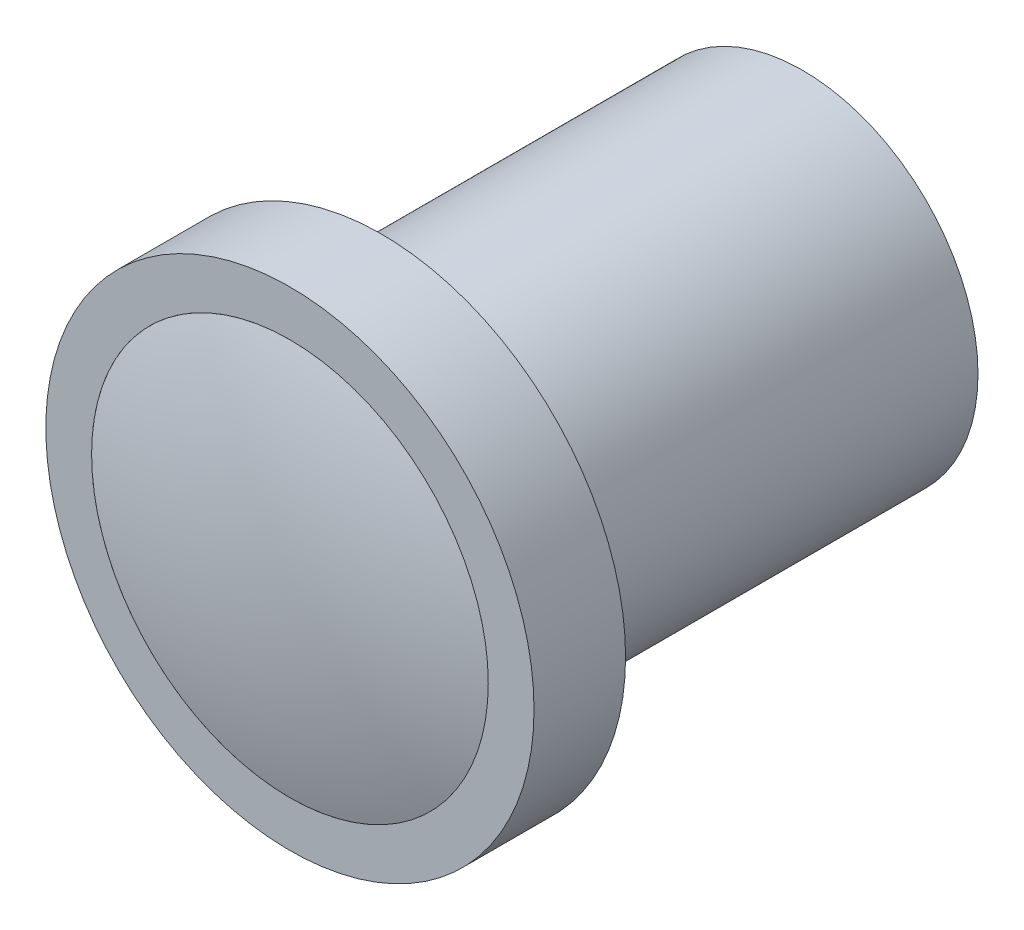
SolidWorks part; units mm, degrees
ref_plane "Front Plane" through (0, 0, 0) normal (0, 0, 1) x (1, 0, 0)
ref_plane "Top Plane" through (0, 0, 0) normal (0, 1, 0) x (1, 0, 0)
ref_plane "Right Plane" through (0, 0, 0) normal (1, 0, 0) x (0, 0, -1)
sketch "Sketch1" plane through (0, 0, 0) normal (0, 0, 1) x (1, 0, 0)
  circle A0 centre (0, 0) radius 5.75
  dimension "D1" = 11.5
extrude "Boss-Extrude1" add sketch "Sketch1" along normal blind 13.8
sketch "Sketch2" plane through (0, 0, 13.8) normal (0, 0, 1) x (1, 0, 0)
  circle A0 centre (0, 0) radius 8
  dimension "D1" = 16
extrude "Boss-Extrude2" add sketch "Sketch2" along normal blind 3
sketch "Sketch3" plane through (0, 0, 16.8) normal (0, 0, 1) x (1, 0, 0)
  circle A0 centre (0, 0) radius 6.5
  circle A1 centre (0, 0) radius 8 construction
  dimension "D1" = 1.5
extrude "Cut-Extrude1" cut sketch "Sketch3" against normal blind 2
sketch "Sketch4" plane through (0, 0, 0) normal (0, 1, 0) x (1, 0, 0)
  line L0 (0, -14.8) -> (0, -17.8)
  line L1 (0, -14.8) -> (6.5, -14.8)
  line L2 (-6.5, -14.8) -> (6.5, -14.8) construction
  line L3 (6.5, -14.8) -> (6.5, -16.8)
  arc A0 (0, -17.8) -> (6.5, -16.8) centre (0, 3.825) ccw
  dimension "D1" = 3
revolve "Revolve1" add sketch "Sketch4" angle 360 about L0
